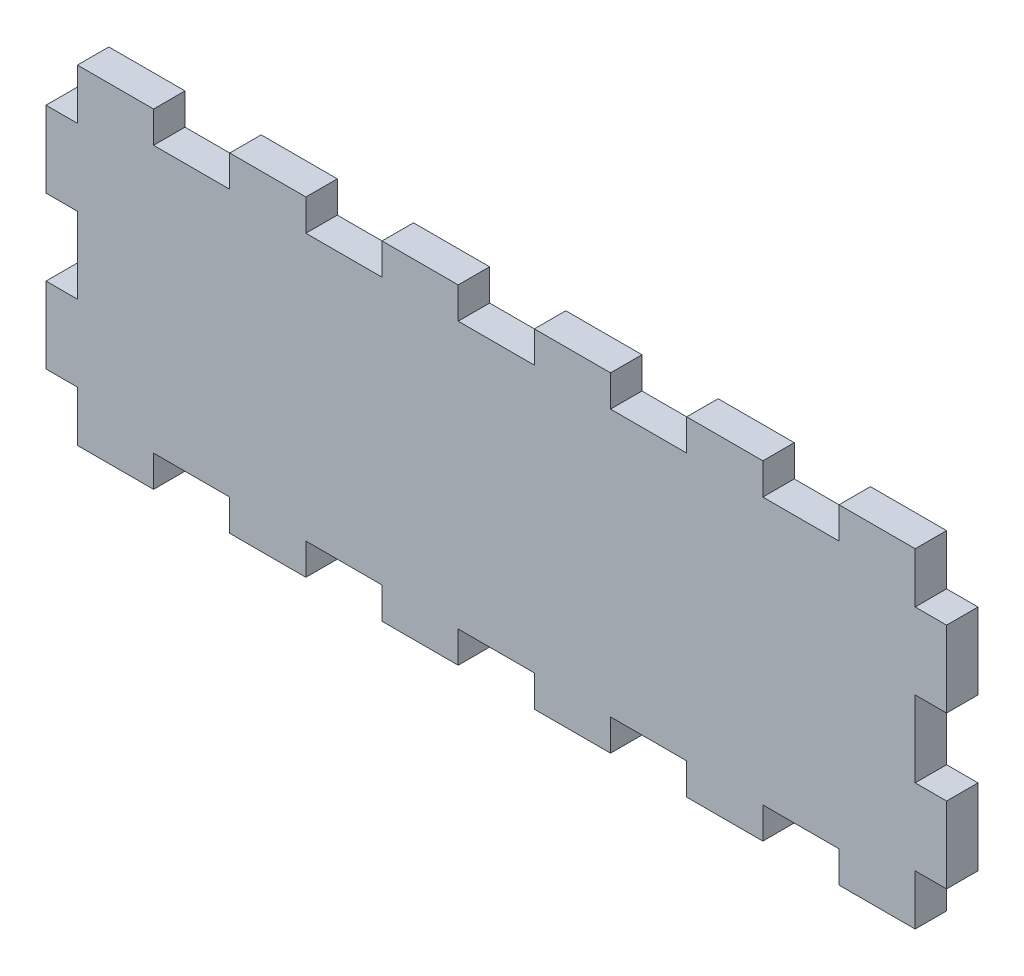
SolidWorks part; units mm, degrees
ref_plane "Plan de face" through (0, 0, 0) normal (0, 0, 1) x (1, 0, 0)
ref_plane "Plan de dessus" through (0, 0, 0) normal (0, 1, 0) x (1, 0, 0)
ref_plane "Plan de droite" through (0, 0, 0) normal (1, 0, 0) x (0, 0, -1)
sketch "Esquisse1" plane through (0, 0, 0) normal (0, 0, 1) x (1, 0, 0)
  line L1 (-47.3, 14) -> (47.3, 14)
  line L2 (-47.3, 14) -> (-47.3, -14)
  line L3 (-47.3, -14) -> (47.3, -14)
  line L4 (47.3, 14) -> (47.3, -14)
  line L5 (-47.3, 14) -> (47.3, -14) construction
  line L6 (-47.3, -14) -> (47.3, 14) construction
  point P0 (0, 0)
  point P10 (0, 14)
  point P11 (-11.6612, 8.264)
  point P12 (-4.0376, 16)
  point P13 (-26.8399, 16)
  point P14 (-28.58, 16)
  point P15 (-7.7259, 16)
  point P16 (-8.0545, 14.1391)
  point P18 (-14.0613, 10.0682)
  dimension "D1" = 28
  dimension "D2" = 94.6
extrude "Boss.-Extru.1" add sketch "Esquisse1" along normal blind 3.3
sketch "Esquisse2" plane through (0, 0, 0) normal (0, 0, -1) x (-1, 0, 0)
  line L0 (-47.3, 14) -> (47.3, 14) construction
  line L1 (-4, 14) -> (4, 14) construction
  line L2 (-4, 14) -> (-4, 17.3) construction
  line L3 (-4, 17.3) -> (4, 17.3) construction
  line L4 (4, 14) -> (4, 17.3)
  line L6 (4, 17.3) -> (12, 17.3)
  line L7 (4, 17.3) -> (4, 14)
  line L8 (4, 14) -> (12, 14)
  line L9 (12, 17.3) -> (12, 14)
  point P4 (0, 14)
  point P7 (0, 14)
  dimension "D1" = 3.3
  dimension "D2" = 8
extrude "Boss.-Extru.2" add sketch "Esquisse2" against normal blind 3.3 contours L7 L6 L9 L8
pattern_linear "Répétition linéaire1" count 3 spacing 16 along (-1, 0, 0) count 4 spacing 16 along (1, 0, 0) of "Boss.-Extru.2"
mirror "Symétrie1" about plane through (0, 0, 0) normal (0, 1, 0) of "Répétition linéaire1", "Boss.-Extru.2"
sketch "Esquisse3" plane through (0, 0, 0) normal (0, 0, -1) x (-1, 0, 0)
  line L1 (-47.3, 4) -> (-44, 4)
  line L2 (-47.3, 4) -> (-47.3, -4)
  line L3 (-47.3, -4) -> (-44, -4)
  line L4 (-44, 4) -> (-44, -4)
  line L5 (-47.3, -14) -> (-47.3, 14) construction
  line L7 (-47.3, 14) -> (-44, 14)
  line L8 (-47.3, 14) -> (-47.3, 12)
  line L9 (-47.3, 12) -> (-44, 12)
  line L10 (-44, 14) -> (-44, 12)
  line L11 (-47.3, -14) -> (-44, -14)
  line L12 (-47.3, -14) -> (-47.3, -12)
  line L13 (-47.3, -12) -> (-44, -12)
  line L14 (-44, -14) -> (-44, -12)
  point P6 (-47.3, 0)
  point P12 (-47.3, 0)
  dimension "D1" = 8
  dimension "D2" = 3.3
  dimension "D3" = 8
  dimension "D4" = 8
extrude "Enlèv. mat.-Extru.1" cut sketch "Esquisse3" against normal blind 3.3
mirror "Symétrie2" about plane through (0, 0, 0) normal (1, 0, 0) of "Enlèv. mat.-Extru.1"
